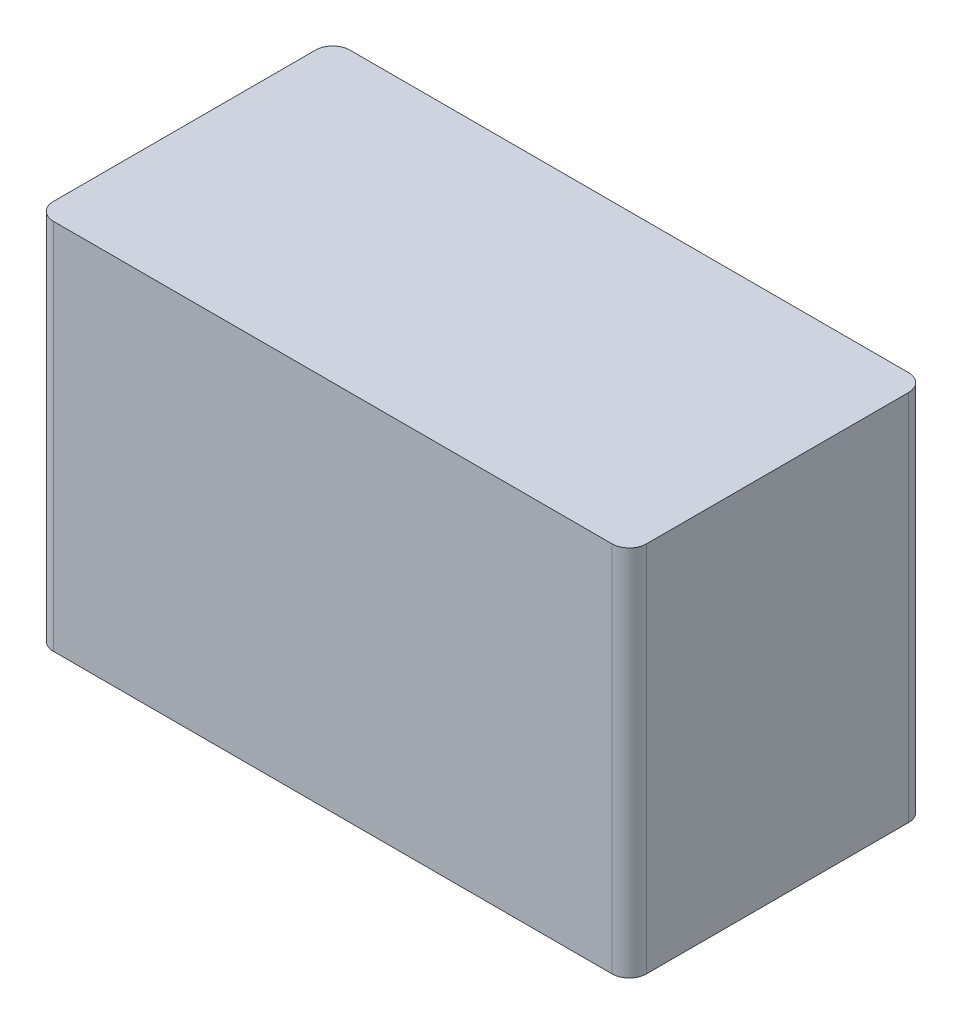
SolidWorks part; units mm, degrees
ref_plane "Alzado" through (0, 0, 0) normal (0, 0, 1) x (1, 0, 0)
ref_plane "Planta" through (0, 0, 0) normal (0, 1, 0) x (1, 0, 0)
ref_plane "Vista lateral" through (0, 0, 0) normal (1, 0, 0) x (0, 0, -1)
sketch "Croquis1" plane through (0, 0, 0) normal (0, 1, 0) x (1, 0, 0)
  line L1 (-20.7, -10.35) -> (20.7, -10.35)
  line L2 (-20.7, -10.35) -> (-20.7, 10.35)
  line L3 (-20.7, 10.35) -> (20.7, 10.35)
  line L4 (20.7, -10.35) -> (20.7, 10.35)
  line L5 (-20.7, -10.35) -> (20.7, 10.35) construction
  line L6 (-20.7, 10.35) -> (20.7, -10.35) construction
  point P0 (0, 0)
  dimension "D1" = 20.7
  dimension "D2" = 41.4
extrude "Saliente-Extruir1" add sketch "Croquis1" along normal blind 26
sketch "Croquis3" plane through (-20.7, 0, 0) normal (-1, 0, 0) x (0, 0, 1)
  line L0 (0, 0) -> (0, 26) construction
  line L1 (-10.35, 0) -> (10.35, 0) construction
  line L2 (-10.35, 26) -> (10.35, 26) construction
  circle A0 centre (0, 10) radius 5.25
  dimension "D1" = 10.5
  dimension "D2" = 10
extrude "Saliente-Extruir2" add sketch "Croquis3" along normal blind 1
fillet "Redondeo1" radius 0.4 2 edges at (-20.7, 10, -5.25) (-21.7, 10, 5.25)
sketch "Croquis5" plane through (-21.7, 0, 0) normal (-1, 0, 0) x (0, 0, 1)
  circle A0 centre (0, 10) radius 4.35
  circle A1 centre (0, 10) radius 4.85 construction
  dimension "D1" = 0.5
extrude "Cortar-Extruir1" cut sketch "Croquis5" against normal blind 0.1
fillet "Redondeo2" radius 1.2 4 edges at (20.7, 13, -10.35) (-20.7, 13, -10.35) (20.7, 13, 10.35) (-20.7, 13, 10.35)
